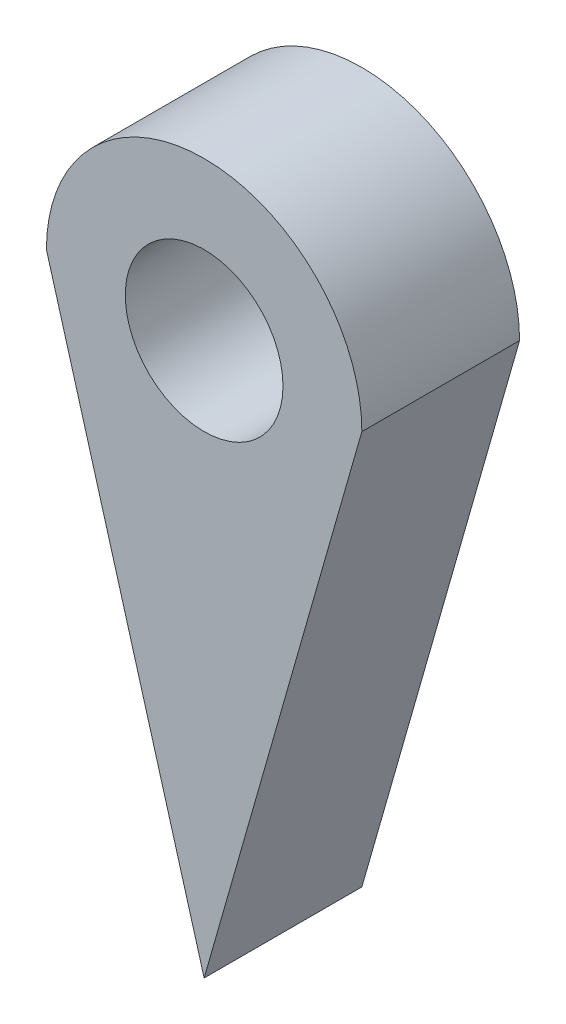
SolidWorks part; units mm, degrees
ref_plane "Front Plane" through (0, 0, 0) normal (0, 0, 1) x (1, 0, 0)
ref_plane "Top Plane" through (0, 0, 0) normal (0, 1, 0) x (1, 0, 0)
ref_plane "Right Plane" through (0, 0, 0) normal (1, 0, 0) x (0, 0, -1)
sketch "Sketch1" plane through (0, 0, 0) normal (0, 0, 1) x (1, 0, 0)
  line L0 (-4, 0) -> (0, -14)
  line L1 (0, -14) -> (4, 0)
  line L2 (-2, 0) -> (-4, 0)
  line L3 (2, 0) -> (4, 0)
  circle A0 centre (0, 0) radius 4
  circle A1 centre (0, 0) radius 2
  dimension "D1" = 4
  dimension "D2" = 8
  dimension "D3" = 14
extrude "Boss-Extrude1" add sketch "Sketch1" along normal blind 4 contours A0 L0 L1 | A1 L2 L0 A0 L1 L3 | A1 L3 A0 L2
